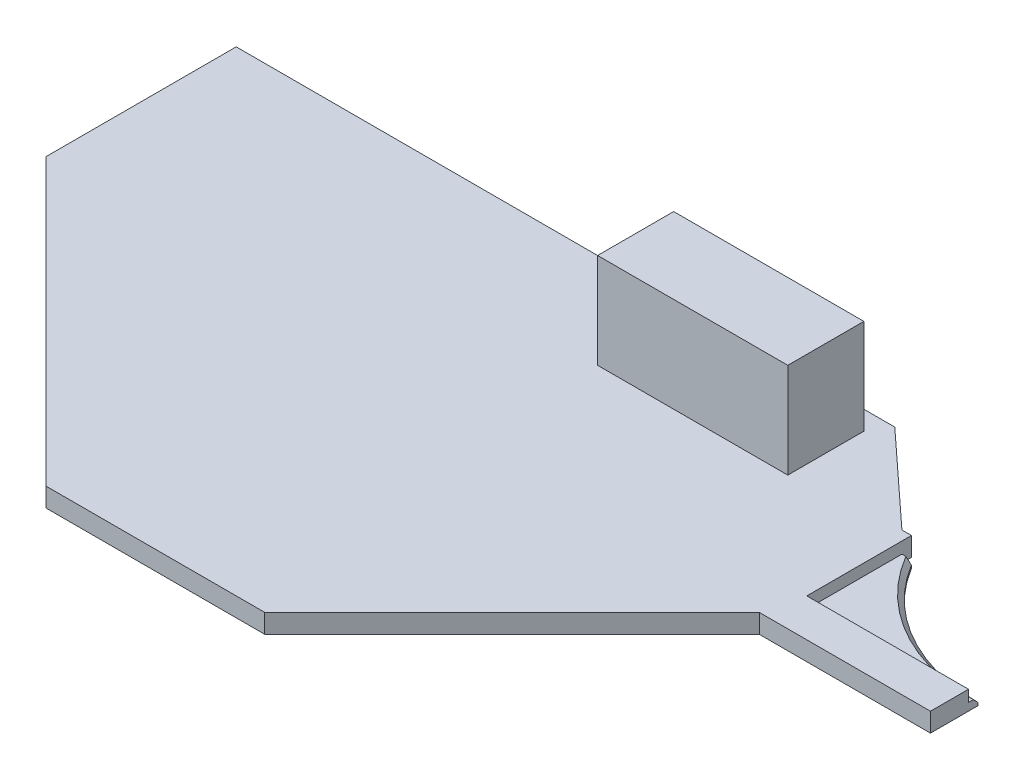
SolidWorks part; units mm, degrees
material "acero"
ref_plane "Alzado" through (0, 0, 0) normal (0, 0, 1) x (1, 0, 0)
ref_plane "Planta" through (0, 0, 0) normal (0, 1, 0) x (1, 0, 0)
ref_plane "Vista lateral" through (0, 0, 0) normal (1, 0, 0) x (0, 0, -1)
sketch "Croquis1" plane through (0, 0, 0) normal (0, 1, 0) x (1, 0, 0)
  line L0 (0, 0) -> (0, 20)
  line L1 (0, 20) -> (69.25, 20)
  line L2 (79, -4) -> (53, -30)
  line L3 (53, -30) -> (30, -30)
  line L4 (30, -30) -> (0, 0)
  line L5 (79, -4) -> (97, -4)
  line L6 (97, -4) -> (97, 11)
  line L9 (69.25, 20) -> (79, 11)
  line L10 (79, 11) -> (97, 11)
  dimension "D1" = 30
  dimension "D2" = 23
  dimension "D3" = 69.25
  dimension "D4" = 30
  dimension "D5" = 18
  dimension "D6" = 18
  dimension "D7" = 9
  dimension "D8" = 20
  dimension "D9" = 97
  dimension "D12" = 15
extrude "Saliente-Extruir2" add sketch "Croquis1" along normal blind 2
sketch "Croquis3" plane through (0, 2, 0) normal (0, 1, 0) x (1, 0, 0)
  line L0 (97, -4) -> (97, 11) construction
  line L1 (80, 11) -> (97, 11)
  line L2 (80, 11) -> (80, 0)
  line L3 (80, 0) -> (97, 0)
  line L4 (97, 11) -> (97, 0)
  line L5 (97, 11) -> (79, 11) construction
  line L6 (79, -4) -> (97, -4) construction
  dimension "D1" = 4
  dimension "D2" = 1
extrude "Cortar-Extruir1" cut sketch "Croquis3" against normal offset from surface (1.2 mm away) 0.8 up to face at (56.0278, 0, 0.6667)
sketch "Croquis4" plane through (0, 0.8, 0) normal (0, 1, 0) x (1, 0, 0)
  line L0 (80, 11) -> (80, 10)
  line L2 (80, 11) -> (80, 0) construction
  line L3 (80, 10) -> (81, 10)
  line L5 (97, 0) -> (97, 1) construction
  line L6 (97, 0) -> (97, 11) construction
  line L7 (97, 1) -> (104.2405, 1) construction
  line L8 (80, 11) -> (97, 11)
  line L9 (97, 11) -> (97, 1)
  arc A0 (81, 10) -> (97, 1) centre (97, 19.7222) ccw
  dimension "D1" = 1
  dimension "D2" = 1
  dimension "D3" = 1
extrude "Cortar-Extruir2" cut sketch "Croquis4" against normal through all
sketch "Croquis5" plane through (0, 2, 0) normal (0, 1, 0) x (1, 0, 0)
  line L0 (68, 18) -> (48, 18)
  line L1 (69.25, 20) -> (0, 20) construction
  line L3 (80, 11) -> (80, 0) construction
  line L5 (48, 18) -> (48, 10)
  line L7 (48, 10) -> (68, 10)
  line L8 (68, 10) -> (68, 18)
  dimension "D1" = 8
  dimension "D2" = 2
  dimension "D3" = 12
  dimension "D4" = 20
extrude "Saliente-Extruir3" add sketch "Croquis5" along normal blind 10
chamfer "Chaflán1" distance 0.5 angle 45 1 edges at (87.8212, 0.8, -3.4044)
